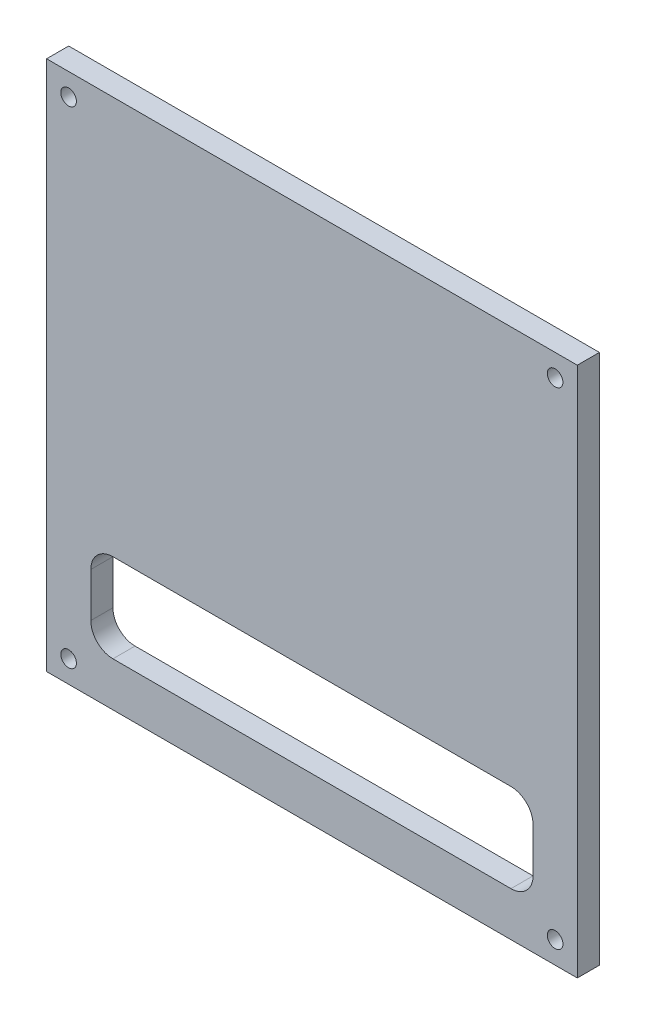
SolidWorks part; units mm, degrees
ref_plane "Front Plane" through (0, 0, 0) normal (0, 0, 1) x (1, 0, 0)
ref_plane "Top Plane" through (0, 0, 0) normal (0, 1, 0) x (1, 0, 0)
ref_plane "Right Plane" through (0, 0, 0) normal (1, 0, 0) x (0, 0, -1)
sketch "Sketch1" plane through (0, 0, 0) normal (0, 0, 1) x (1, 0, 0)
  line L1 (-316.3747, 235.8515) -> (-163.9747, 235.8515)
  line L2 (-316.3747, 235.8515) -> (-316.3747, 121.5515)
  line L4 (-163.9747, 235.8515) -> (-163.9747, 121.5515)
  line L6 (-316.3747, 121.5515) -> (-316.3747, 83.4515)
  line L7 (-316.3747, 83.4515) -> (-163.9747, 83.4515)
  line L8 (-163.9747, 121.5515) -> (-163.9747, 83.4515)
  line L9 (-303.6747, 96.1515) -> (-176.6747, 96.1515)
  line L10 (-303.6747, 96.1515) -> (-303.6747, 121.5515)
  line L11 (-303.6747, 121.5515) -> (-176.6747, 121.5515)
  line L12 (-176.6747, 96.1515) -> (-176.6747, 121.5515)
  arc A0 (-303.6747, 115.2015) -> (-297.3247, 121.5515) centre (-297.3247, 115.2015) cw
  arc A1 (-303.6747, 102.5015) -> (-297.3247, 96.1515) centre (-297.3247, 102.5015) ccw
  arc A2 (-183.0247, 96.1515) -> (-176.6747, 102.5015) centre (-183.0247, 102.5015) ccw
  arc A3 (-183.0247, 121.5515) -> (-176.6747, 115.2015) centre (-183.0247, 115.2015) cw
  point P10 (-240.1747, 96.1515)
  point P11 (-240.1747, 83.4515)
  dimension "D7" = 6.35
  dimension "D1" = 152.4
  dimension "D2" = 114.3
  dimension "D3" = 152.4
  dimension "D4" = 12.7
  dimension "D5" = 127
  dimension "D6" = 25.4
extrude "Boss-Extrude1" add sketch "Sketch1" along normal blind 6.35 contours L8 L4 L1 L2 L6 L7 L12 L9 L10 L11 | L10 A0 L11 | A1 L10 L9 | L11 A3 L12 | A2 L9 L12
hole_wizard "#8 Clearance Hole2" positions "Sketch2" profile "Sketch3" hole size "#8" standard "ANSI Inch" end condition through all
sketch "Sketch2" plane through (0, 0, 6.35) normal (0, 0, 1) x (1, 0, 0)
  line L4 (-316.3747, 235.8515) -> (-316.3747, 83.4515) construction
  line L5 (-316.3747, 231.3515) -> (-310.0515, 231.3515)
  line L7 (-310.0515, 235.8515) -> (-310.0515, 229.5179)
  line L8 (-316.3747, 235.8515) -> (-163.9747, 235.8515) construction
  point P16 (-310.0515, 229.5179)
sketch "Sketch3" plane through (-310.0515, 229.5179, 6.35) normal (1, 0, 0) x (0, -1, 0)
  line L0 (0, 0) -> (0, 6.35)
  line L1 (0, 6.35) -> (2.2479, 6.35)
  line L2 (2.2479, 6.35) -> (2.2479, 0)
  line L5 (2.2479, 0) -> (0, 0)
  line L11 (0, -6.35) -> (0, 107.95) construction
  dimension "Thru Hole Dia." = 4.4958
  dimension "Thru Hole Depth" = 6.35
pattern_linear "LPattern1" count 2 spacing 139.7 along (0, -1, 0) count 2 spacing 139.7 along (1, 0, 0) of "#8 Clearance Hole2"
